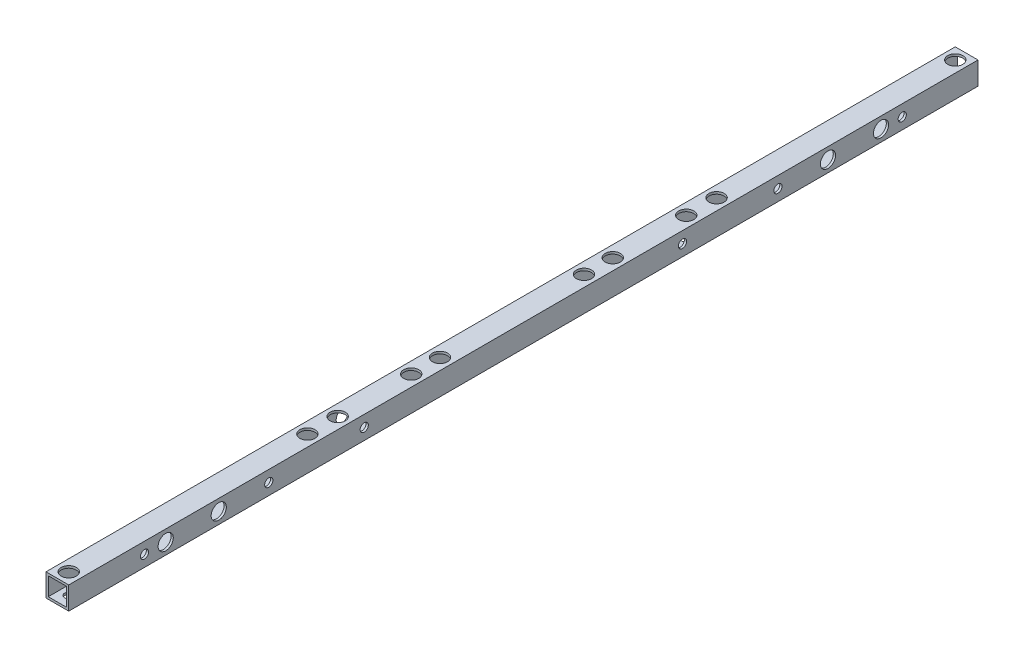
SolidWorks part; units mm, degrees
material "6063-T5"
ref_plane "正面" through (0, 0, 0) normal (0, 0, 1) x (1, 0, 0)
ref_plane "平面" through (0, 0, 0) normal (0, 1, 0) x (1, 0, 0)
ref_plane "右側面" through (0, 0, 0) normal (1, 0, 0) x (0, 0, -1)
sketch "ｽｹｯﾁ1" plane through (0, 0, 0) normal (0, 0, 1) x (1, 0, 0)
  line L1 (-7.5, -7.5) -> (7.5, -7.5)
  line L2 (-7.5, -7.5) -> (-7.5, 7.5)
  line L3 (-7.5, 7.5) -> (7.5, 7.5)
  line L4 (7.5, -7.5) -> (7.5, 7.5)
  line L5 (-7.5, -7.5) -> (7.5, 7.5) construction
  line L6 (-7.5, 7.5) -> (7.5, -7.5) construction
  line L7 (-6, -6) -> (6, -6)
  line L8 (-6, -6) -> (-6, 6)
  line L9 (-6, 6) -> (6, 6)
  line L10 (6, -6) -> (6, 6)
  line L11 (-6, -6) -> (6, 6) construction
  line L12 (-6, 6) -> (6, -6) construction
  point P0 (0, 0)
  point P6 (0, 0)
  dimension "D1" = 1.5
  dimension "D2" = 15
  dimension "D3" = 15
extrude "ﾎﾞｽ - 押し出し1" add sketch "ｽｹｯﾁ1" along normal blind 600
sketch "ｽｹｯﾁ3" plane through (0, 7.5, 0) normal (0, 1, 0) x (1, 0, 0)
  line L2 (7.5, -600) -> (7.5, 0) construction
  line L3 (7.5, 0) -> (-7.5, 0) construction
  circle A1 centre (0, -7.5) radius 2.7
  circle A6 centre (0, -592.5) radius 2.7
  circle A8 centre (0, -233.5) radius 2.7
  circle A9 centre (0, -366.5) radius 2.7
  point P10 (7.5, -300)
  dimension "D2" = 7.5
  dimension "D3" = 5.4
  dimension "D7" = 133
  dimension "D8" = 5.4
  dimension "D9" = 7.5
  dimension "D11" = 7.5
  dimension "D4" = 7.5
  dimension "D5" = 5.4
  dimension "D10" = 5.4
  dimension "D12" = 7.5
  dimension "D13" = 7.5
  dimension "D6" = 66.5
extrude "ｶｯﾄ - 押し出し2" cut sketch "ｽｹｯﾁ3" against normal blind 25
sketch "ｽｹｯﾁ4" plane through (7.5, 0, 0) normal (1, 0, 0) x (0, 0, -1)
  line L0 (-600, -7.5) -> (-600, 7.5) construction
  line L1 (-600, -7.5) -> (0, -7.5) construction
  line L2 (0, -7.5) -> (0, 7.5) construction
  line L3 (-300, 7.5) -> (-300, -7.5) construction
  line L4 (-600, 7.5) -> (0, 7.5) construction
  circle A0 centre (-536, 0) radius 2.7
  circle A1 centre (-501, 0) radius 2.7
  circle A2 centre (-99, 0) radius 2.7
  circle A3 centre (-64, 0) radius 2.7
  circle A4 centre (-468, 0) radius 2.7
  circle A8 centre (-550, 0) radius 2.7
  circle A9 centre (-405, 0) radius 2.7
  circle A11 centre (-195, 0) radius 2.7
  circle A12 centre (-50, 0) radius 2.7
  circle A13 centre (-132, 0) radius 2.7
  dimension "D2" = 7.5
  dimension "D3" = 5.4
  dimension "D5" = 35
  dimension "D7" = 64
  dimension "D9" = 132
  dimension "D11" = 145
  dimension "D8" = 5.4
  dimension "D10" = 7.5
  dimension "D1" = 64
  dimension "D12" = 63
  dimension "D4" = 2
  dimension "D6" = 2
extrude "ｶｯﾄ - 押し出し3" cut sketch "ｽｹｯﾁ4" against normal blind 20
sketch "ｽｹｯﾁ6" plane through (0, 7.5, 0) normal (0, 1, 0) x (1, 0, 0)
  line L0 (7.5, -600) -> (7.5, 0) construction
  line L1 (7.5, -600) -> (-7.5, -600) construction
  line L2 (7.5, 0) -> (-7.5, 0) construction
  circle A0 centre (0, -435) radius 2.7
  circle A1 centre (0, -415) radius 2.7
  circle A2 centre (0, -165) radius 2.7
  circle A3 centre (0, -185) radius 2.7
  circle A4 centre (0, -347.5) radius 2.7
  circle A5 centre (0, -252.5) radius 2.7
  point P21 (7.5, -300)
  dimension "D1" = 5.4
  dimension "D2" = 7.5
  dimension "D3" = 165
  dimension "D5" = 20
  dimension "D7" = 165
  dimension "D8" = 95
  dimension "D9" = 47.5
  dimension "D4" = 2
  dimension "D6" = 2
extrude "ｶｯﾄ - 押し出し5" cut sketch "ｽｹｯﾁ6" against normal blind 30
sketch "ｽｹｯﾁ7" plane through (0, 7.5, 0) normal (0, 1, 0) x (1, 0, 0)
  circle A0 centre (0, -592.5) radius 5
  circle A3 centre (0, -7.5) radius 5
  circle A6 centre (0, -185) radius 5
  circle A7 centre (0, -165) radius 5
  circle A8 centre (0, -435) radius 5
  circle A9 centre (0, -415) radius 5
  circle A12 centre (0, -366.5) radius 5
  circle A13 centre (0, -233.5) radius 5
  circle A14 centre (0, -252.5) radius 5
  circle A15 centre (0, -347.5) radius 5
  dimension "D1" = 10
  dimension "D4" = 10
  dimension "D5" = 10
  dimension "D6" = 10
  dimension "D7" = 10
  dimension "D8" = 10
  dimension "D9" = 10
  dimension "D10" = 10
extrude "ｶｯﾄ - 押し出し6" cut sketch "ｽｹｯﾁ7" against normal blind 10
sketch "ｽｹｯﾁ8" plane through (7.5, 0, 0) normal (1, 0, 0) x (0, 0, -1)
  circle A0 centre (-64, 0) radius 5
  circle A1 centre (-99, 0) radius 5
  circle A2 centre (-536, 0) radius 5
  circle A3 centre (-501, 0) radius 5
  dimension "D1" = 10
  dimension "D2" = 10
  dimension "D3" = 10
  dimension "D4" = 10
extrude "ｶｯﾄ - 押し出し7" cut sketch "ｽｹｯﾁ8" against normal blind 10
sketch "ｽｹｯﾁ9" plane through (-7.5, 0, 0) normal (-1, 0, 0) x (0, 0, 1)
  circle A3 centre (468, 0) radius 5
  circle A4 centre (405, 0) radius 5
  circle A5 centre (550, 0) radius 5
  circle A6 centre (195, 0) radius 5
  circle A7 centre (50, 0) radius 5
  circle A8 centre (50, 0) radius 2.7 construction
  circle A9 centre (132, 0) radius 5
  dimension "D1" = 10
extrude "ｶｯﾄ - 押し出し8" cut sketch "ｽｹｯﾁ9" against normal blind 10
equation "\"D9@ｽｹｯﾁ6\"= \"D8@ｽｹｯﾁ6\" / 2"
